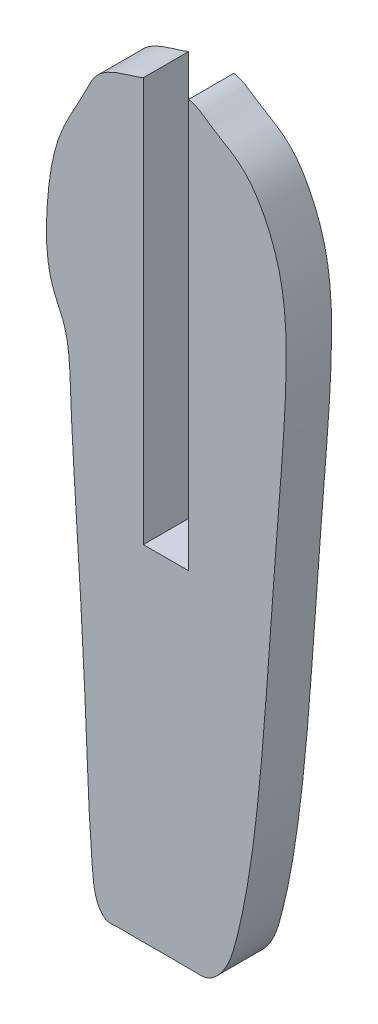
SolidWorks part; units mm, degrees
ref_plane "Front Plane" through (0, 0, 0) normal (0, 0, 1) x (1, 0, 0)
ref_plane "Top Plane" through (0, 0, 0) normal (0, 1, 0) x (1, 0, 0)
ref_plane "Right Plane" through (0, 0, 0) normal (1, 0, 0) x (0, 0, -1)
sketch "Sketch1" plane through (0, 0, 0) normal (0, 0, 1) x (1, 0, 0)
  line L0 (-28.8298, 0) -> (35.4255, 0) construction
  line L1 (0, 37.1809) -> (0, -44.5213) construction
  line L2 (2.2, 16.2799) -> (2.2, -10.7088)
  line L3 (-7.5, 16.5426) -> (7.5, 16.5426) construction
  line L4 (-7.5, 16.5426) -> (-7.5, -33.4574) construction
  line L5 (-7.5, -33.4574) -> (7.5, -33.4574) construction
  line L6 (7.5, 16.5426) -> (7.5, -33.4574) construction
  line L7 (2.2, -10.7088) -> (-0.8, -10.7088)
  line L8 (-0.8, -10.7088) -> (-0.8, 16.0186)
  spline S0 degree 3 poles (-0.8, 16.0186) (-1.1375, 15.8568) (-3.865, 15.1866) (-4.4643, 13.377) (-6.5305, 10.1605) (-7.0963, 6.8155) (-7.2767, 3.65) (-7.0103, 1.2221) (-6.0386, -0.5009) (-5.6723, -2.2484) (-5.576, -5.9641) (-5.1213, -12.7482) (-4.587, -21.7777) (-4.3983, -28.5426) (-4.0105, -32.494) (-3.4929, -33.5812) (-2.4822, -33.4323) (-1.9755, -33.4536) (-1.143, -33.4666) (-0.5961, -33.4776) (0, -33.4574) knots 0.027253 0.027253 0.027253 0.027253 0.046559 0.096385 0.158729 0.228186 0.271982 0.32308 0.3513 0.373138 0.414663 0.543428 0.725126 0.882497 0.894014 0.929959 0.943401 0.960683 0.966343 1 1 1 1
  spline S1 degree 3 poles (2.2, 16.2799) (2.9631, 16.0866) (3.38, 15.5594) (5.775, 14.3546) (7.3746, 12.063) (8.5516, 8.6726) (8.7339, 3.819) (8.2811, -2.6741) (7.5344, -11.8537) (6.9584, -21.3736) (5.8209, -28.7487) (4.7756, -32.3039) (3.6574, -33.423) (2.7282, -33.4865) (2.155, -33.4569) (1.1177, -33.4577) (0.4763, -33.4612) (0, -33.4574) knots 0.025935 0.025935 0.025935 0.025935 0.066183 0.102078 0.144599 0.209521 0.281427 0.391334 0.54222 0.751599 0.880094 0.919234 0.943979 0.94911 0.968166 0.973493 1 1 1 1
  dimension "D1" = 50
  dimension "D2" = 15
  dimension "D3" = 7.5
  dimension "D4" = 3
  dimension "D5" = 0.8
extrude "Boss-Extrude2" add sketch "Sketch1" along normal blind 3
